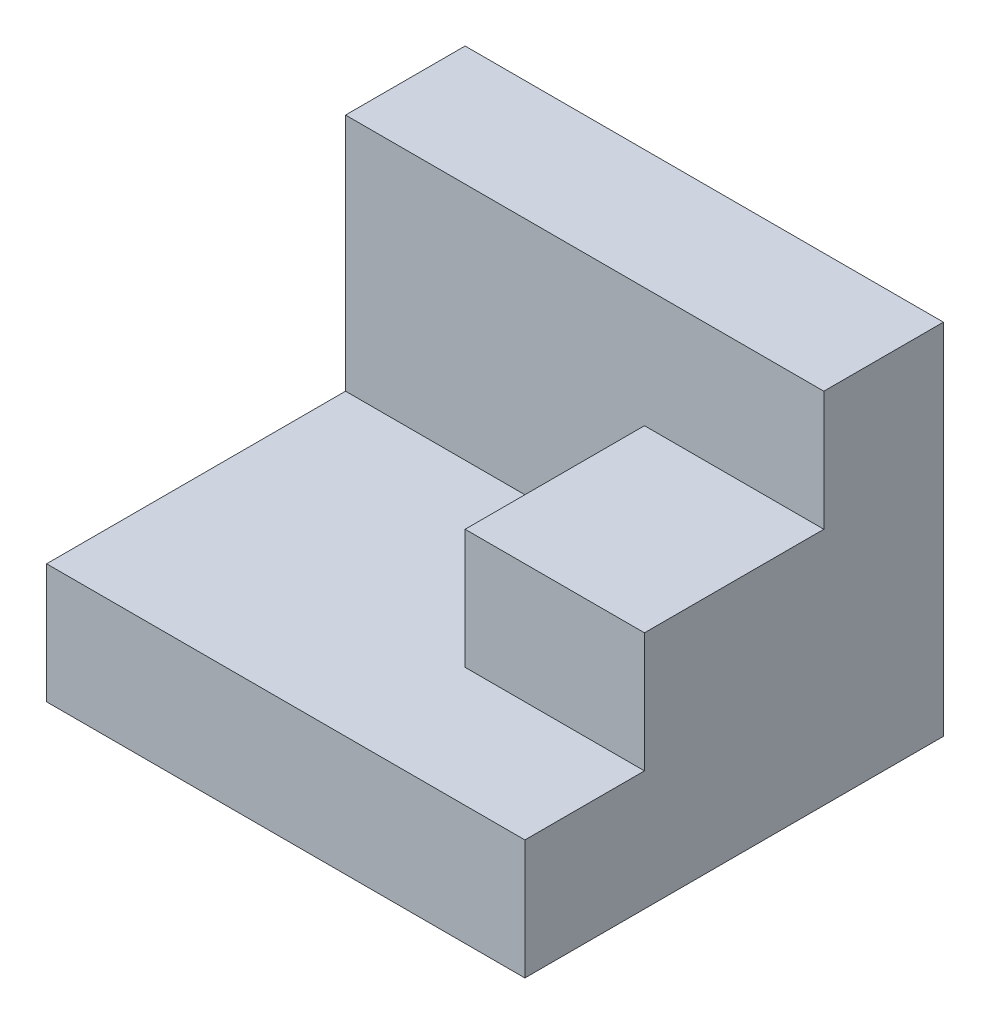
SolidWorks part; units mm, degrees
ref_plane "Front Plane" through (0, 0, 0) normal (0, 0, 1) x (1, 0, 0)
ref_plane "Top Plane" through (0, 0, 0) normal (0, 1, 0) x (1, 0, 0)
ref_plane "Right Plane" through (0, 0, 0) normal (1, 0, 0) x (0, 0, -1)
sketch "Sketch1" plane through (0, 0, 0) normal (1, 0, 0) x (0, 0, -1)
  line L0 (10.106, 12.7731) -> (10.106, -17.2269)
  line L1 (10.106, -17.2269) -> (-24.894, -17.2269)
  line L2 (-24.894, -17.2269) -> (-24.894, -7.2269)
  line L3 (-24.894, -7.2269) -> (0.106, -7.2269)
  line L4 (0.106, -7.2269) -> (0.106, 12.7731)
  line L5 (0.106, 12.7731) -> (10.106, 12.7731)
  dimension "D1" = 30
  dimension "D2" = 35
  dimension "D3" = 10
  dimension "D4" = 10
extrude "Boss-Extrude1" add sketch "Sketch1" against normal blind 40
sketch "Sketch2" plane through (0, 0, 0) normal (1, 0, 0) x (0, 0, -1)
  line L0 (0.106, -7.2269) -> (-14.894, -7.2269)
  line L1 (0.106, -7.2269) -> (-24.894, -7.2269) construction
  line L2 (-14.894, -7.2269) -> (-14.894, 2.7731)
  line L3 (-14.894, 2.7731) -> (0.106, 2.7731)
  line L4 (0.106, 12.7731) -> (0.106, -7.2269) construction
  line L5 (0.106, 2.7731) -> (0.106, -7.2269)
  dimension "D1" = 15
  dimension "D2" = 10
extrude "Boss-Extrude2" add sketch "Sketch2" against normal blind 15
